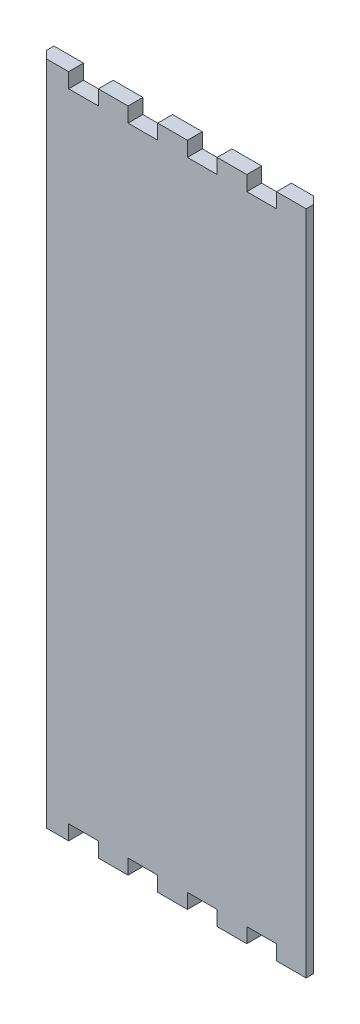
SolidWorks part; units mm, degrees
ref_plane "Front Plane" through (0, 0, 0) normal (0, 0, 1) x (1, 0, 0)
ref_plane "Top Plane" through (0, 0, 0) normal (0, 1, 0) x (1, 0, 0)
ref_plane "Right Plane" through (0, 0, 0) normal (1, 0, 0) x (0, 0, -1)
sketch "Model" plane through (0, 0, 0) normal (0, 0, 1) x (1, 0, 0)
  line L620 (861.0219, 23.2006) -> (866.7039, 23.2006)
  line L621 (866.7039, 23.2006) -> (866.7039, 28.9154)
  line L622 (866.7039, 28.9154) -> (878.1339, 28.9154)
  line L623 (878.1339, 28.9154) -> (878.1339, 23.2006)
  line L624 (878.1339, 23.2006) -> (889.569, 23.2006)
  line L625 (889.569, 23.2006) -> (889.569, 28.9154)
  line L626 (889.569, 28.9154) -> (900.9939, 28.9154)
  line L627 (900.9939, 28.9154) -> (900.9939, 23.2006)
  line L628 (900.9939, 23.2006) -> (912.429, 23.2006)
  line L629 (912.429, 23.2006) -> (912.429, 28.9154)
  line L630 (912.429, 28.9154) -> (923.8539, 28.9154)
  line L631 (923.8539, 28.9154) -> (923.8539, 23.2006)
  line L632 (923.8539, 23.2006) -> (935.2839, 23.2006)
  line L633 (935.2839, 23.2006) -> (935.2839, 28.9154)
  line L634 (935.2839, 28.9154) -> (946.719, 28.9154)
  line L635 (946.719, 28.9154) -> (946.719, 23.2006)
  line L636 (946.719, 23.2006) -> (958.1159, 23.2006)
  line L637 (958.1159, 23.2006) -> (958.1159, 279.6311)
  line L638 (958.1159, 279.6311) -> (946.719, 279.6311)
  line L639 (946.719, 279.6311) -> (946.719, 273.9161)
  line L640 (946.719, 273.9161) -> (935.2839, 273.9161)
  line L641 (935.2839, 273.9161) -> (935.2839, 279.6311)
  line L642 (935.2839, 279.6311) -> (923.8539, 279.6311)
  line L643 (923.8539, 279.6311) -> (923.8539, 273.9161)
  line L644 (923.8539, 273.9161) -> (912.429, 273.9161)
  line L645 (912.429, 273.9161) -> (912.429, 279.6311)
  line L646 (912.429, 279.6311) -> (900.9939, 279.6311)
  line L647 (900.9939, 279.6311) -> (900.9939, 273.9161)
  line L648 (900.9939, 273.9161) -> (889.569, 273.9161)
  line L649 (889.569, 273.9161) -> (889.569, 279.6311)
  line L650 (889.569, 279.6311) -> (878.1339, 279.6311)
  line L651 (878.1339, 279.6311) -> (878.1339, 273.9161)
  line L652 (878.1339, 273.9161) -> (866.7039, 273.9161)
  line L653 (866.7039, 273.9161) -> (866.7039, 279.6311)
  line L654 (866.7039, 279.6311) -> (855.3069, 279.6311)
  line L655 (855.3069, 279.6311) -> (855.3069, 23.2006)
  line L656 (855.3069, 23.2006) -> (861.0219, 23.2006)
extrude "Boss-Extrude1" add sketch "Model" along normal blind 5.715
sketch "Sketch1" plane through (0, 23.2006, 0) normal (0, -1, 0) x (1, 0, 0)
  line L0 (855.3069, 2.8575) -> (858.1644, 5.715)
  line L1 (855.3069, 5.715) -> (855.3069, 0) construction
  line L2 (855.3069, 5.715) -> (866.7039, 5.715) construction
  line L3 (958.1159, 2.8575) -> (955.2584, 0)
  line L4 (958.1159, 5.715) -> (958.1159, 0) construction
  line L5 (946.719, 0) -> (958.1159, 0) construction
  line L6 (855.3069, 2.8575) -> (855.3069, 5.715)
  line L7 (855.3069, 5.715) -> (858.1644, 5.715)
  line L8 (955.2584, 0) -> (958.1159, 0)
  line L9 (958.1159, 0) -> (958.1159, 2.8575)
  dimension "D1" = 2.8575
extrude "Cut-Extrude1" cut sketch "Sketch1" against normal through all
